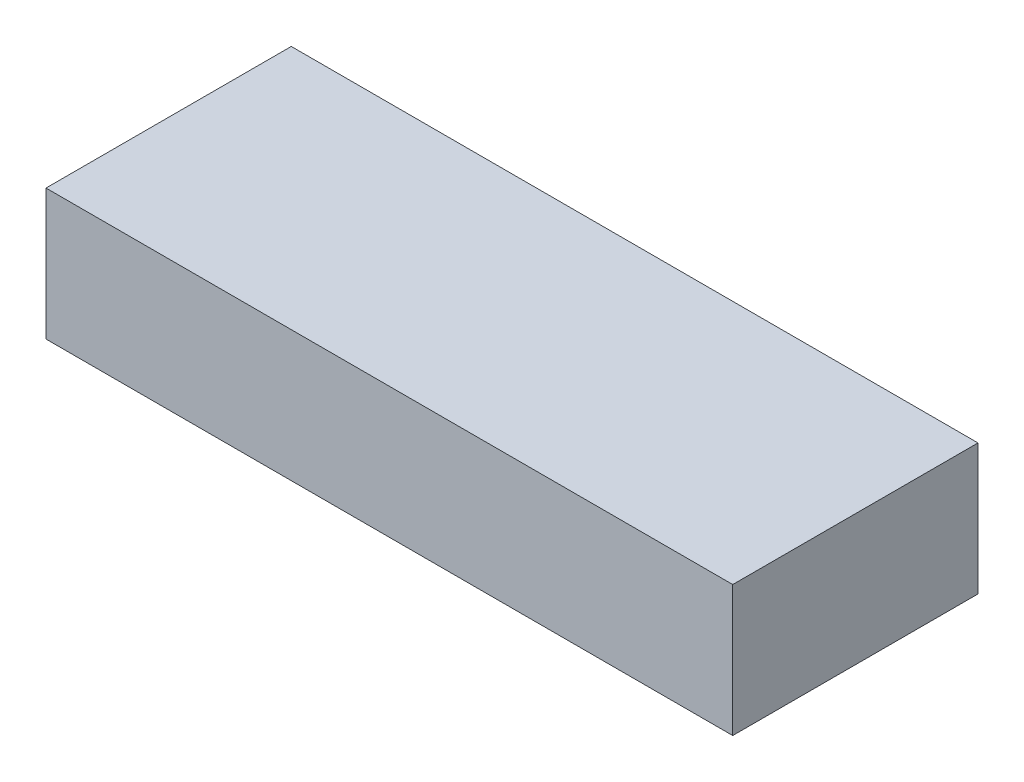
SolidWorks part; units mm, degrees
ref_plane "Front Plane" through (0, 0, 0) normal (0, 0, 1) x (1, 0, 0)
ref_plane "Top Plane" through (0, 0, 0) normal (0, 1, 0) x (1, 0, 0)
ref_plane "Right Plane" through (0, 0, 0) normal (1, 0, 0) x (0, 0, -1)
sketch "Sketch1" plane through (0, 0, 0) normal (0, 1, 0) x (1, 0, 0)
  line L1 (66.675, -23.8125) -> (-66.675, -23.8125)
  line L2 (66.675, -23.8125) -> (66.675, 23.8125)
  line L3 (66.675, 23.8125) -> (-66.675, 23.8125)
  line L4 (-66.675, -23.8125) -> (-66.675, 23.8125)
  line L5 (66.675, -23.8125) -> (-66.675, 23.8125) construction
  line L6 (66.675, 23.8125) -> (-66.675, -23.8125) construction
  point P0 (0, 0)
  dimension "D1" = 133.35
  dimension "D2" = 47.625
extrude "Boss-Extrude1" add sketch "Sketch1" along normal blind 25.4
